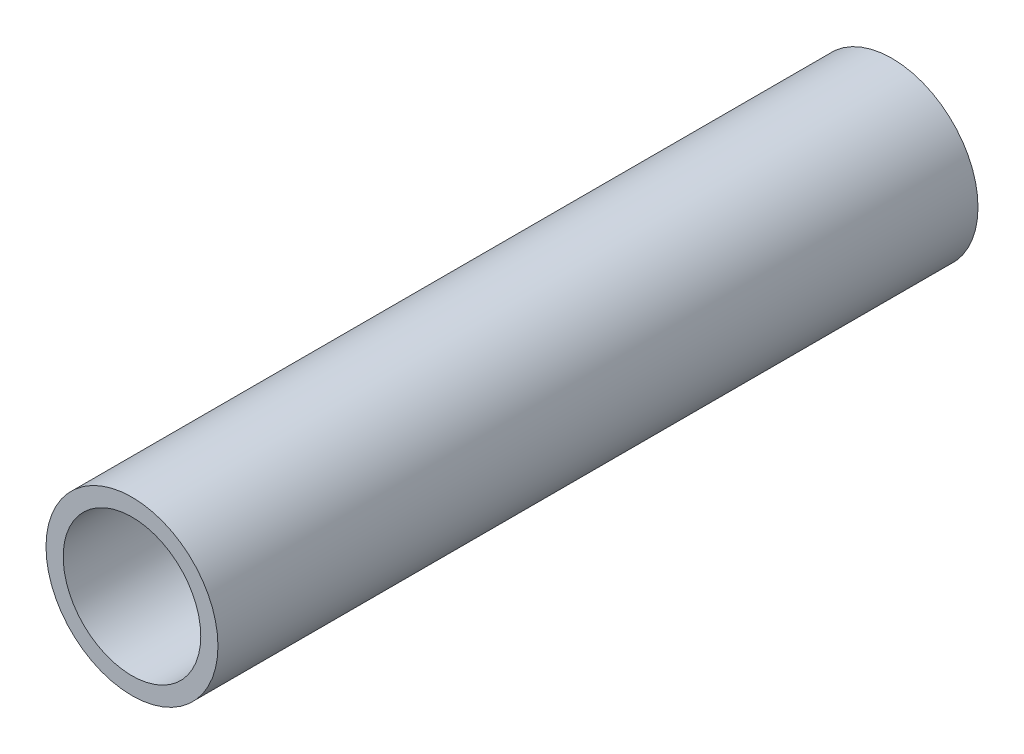
SolidWorks part; units mm, degrees
material "Hexcel AS4C (3000 Filaments)"
ref_plane "Front" through (0, 0, 0) normal (0, 0, 1) x (1, 0, 0)
ref_plane "Top" through (0, 0, 0) normal (0, 1, 0) x (1, 0, 0)
ref_plane "Right" through (0, 0, 0) normal (1, 0, 0) x (0, 0, -1)
sketch "Sketch1" plane through (0, 0, 0) normal (0, 0, 1) x (1, 0, 0)
  circle A0 centre (0, 0) radius 4
  circle A1 centre (0, 0) radius 5
  dimension "D1" = 10
  dimension "D2" = 1
extrude "Boss-Extrude1" add sketch "Sketch1" along normal blind 44.2
